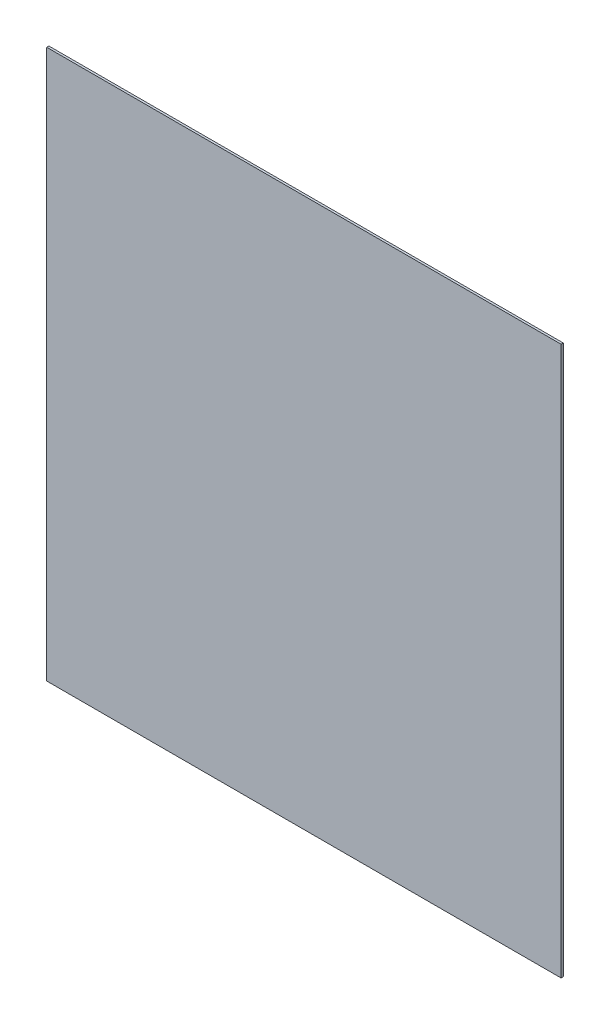
SolidWorks part; units mm, degrees
material "Mahogany"
ref_plane "Front Plane" through (0, 0, 0) normal (0, 0, 1) x (1, 0, 0)
ref_plane "Top Plane" through (0, 0, 0) normal (0, 1, 0) x (1, 0, 0)
ref_plane "Right Plane" through (0, 0, 0) normal (1, 0, 0) x (0, 0, -1)
sketch "Sketch1" plane through (0, 0, 0) normal (0, 0, 1) x (1, 0, 0)
  line L1 (-372.5, 397.5) -> (372.5, 397.5)
  line L2 (-372.5, 397.5) -> (-372.5, -397.5)
  line L3 (-372.5, -397.5) -> (372.5, -397.5)
  line L4 (372.5, 397.5) -> (372.5, -397.5)
  line L5 (-372.5, 397.5) -> (372.5, -397.5) construction
  line L6 (-372.5, -397.5) -> (372.5, 397.5) construction
  point P0 (0, 0)
  dimension "D1" = 745
  dimension "D2" = 795
extrude "Boss-Extrude1" add sketch "Sketch1" along normal blind 3.175
equation "\"W\"= 1700"
equation "\"L\"= 760"
equation "\"H\"= 810"
equation "\"ARM_BOLT_SPACING\"= 166"
equation "\"ARM_TO_WALL\"= 300"
equation "\"D1@Sketch1\"=\"L\"-15"
equation "\"D2@Sketch1\"=\"H\"-(15)"
